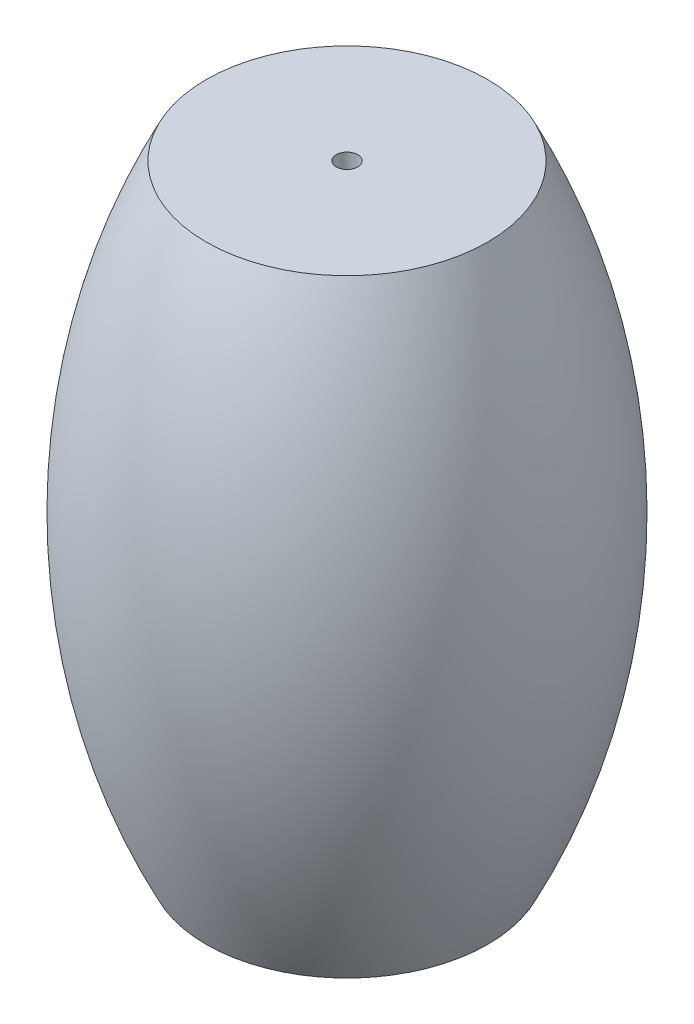
SolidWorks part; units mm, degrees
ref_plane "Front Plane" through (0, 0, 0) normal (0, 0, 1) x (1, 0, 0)
ref_plane "Top Plane" through (0, 0, 0) normal (0, 1, 0) x (1, 0, 0)
ref_plane "Right Plane" through (0, 0, 0) normal (1, 0, 0) x (0, 0, -1)
sketch "Sketch1" plane through (0, 0, 0) normal (0, 0, 1) x (1, 0, 0)
  line L0 (6.09, 0) -> (0, 0)
  line L1 (0, 0) -> (0, 28.477)
  line L2 (0, 28.477) -> (6.09, 28.477)
  line L3 (0, 0) -> (-0.5, 0)
  line L4 (-0.5, 0) -> (-0.5, 29.6096)
  arc A1 (6.09, 0) -> (6.09, 28.477) centre (-22.5677, 14.2385) ccw
  dimension "D1" = 6.09
  dimension "D4" = 64
  dimension "D2" = 28.477
  dimension "D3" = 6.09
  dimension "D5" = 0.5
revolve "Revolve1" add sketch "Sketch1" angle 360 about L4
